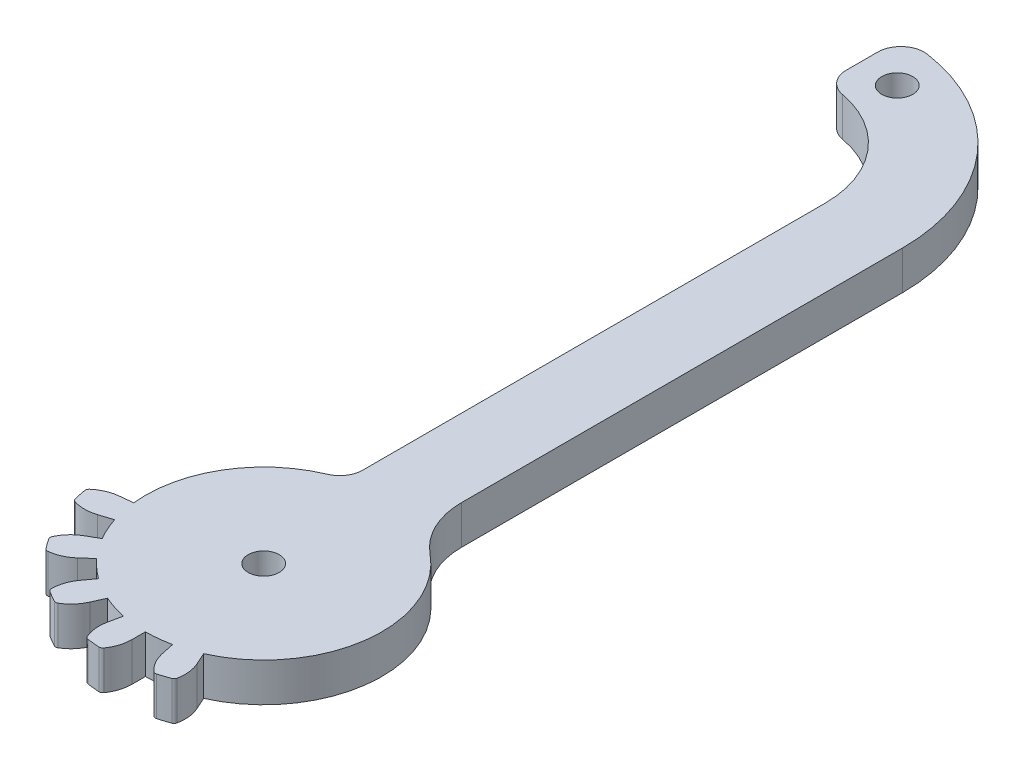
SolidWorks part; units mm, degrees
ref_plane "Front Plane" through (0, 0, 0) normal (0, 0, 1) x (1, 0, 0)
ref_plane "Top Plane" through (0, 0, 0) normal (0, 1, 0) x (1, 0, 0)
ref_plane "Right Plane" through (0, 0, 0) normal (1, 0, 0) x (0, 0, -1)
sketch "Sketch1" plane through (0, 0, 0) normal (0, 1, 0) x (1, 0, 0)
  line L1 (-4.0461, -7.1956) -> (-4.0461, 54.5906)
  line L2 (5.9539, -7.8588) -> (5.9539, 54.5906)
  line L3 (-15.1764, -23.5045) -> (-16.9069, -23.6864)
  line L4 (-14.5131, -26.625) -> (-16.168, -27.1627)
  line L6 (-13.2155, -29.5394) -> (-14.7224, -30.4094)
  line L7 (-11.3404, -32.1203) -> (-12.6335, -33.2846)
  line L11 (-8.9696, -34.255) -> (-9.9923, -35.6627)
  line L12 (-6.2068, -35.8501) -> (-6.9145, -37.4397)
  line L14 (-17.5461, 78.0906) -> (-17.5461, 68.0906)
  line L15 (-3.1727, -36.8359) -> (-3.5345, -38.5379)
  line L16 (0, -37.1694) -> (0, -38.9094)
  line L19 (3.1727, -36.8359) -> (3.5345, -38.5379)
  line L20 (6.2068, -35.8501) -> (6.9145, -37.4397)
  line L29 (13.2155, -29.5394) -> (14.7224, -30.4094) [skipped]
  line L30 (11.3404, -32.1203) -> (12.6335, -33.2846) [skipped]
  line L31 (8.9696, -34.255) -> (9.9923, -35.6627) [skipped]
  line L32 (14.5131, -26.625) -> (16.168, -27.1627) [skipped]
  arc A0 (-15.26, -21.9094) -> (-15.1764, -23.5045) centre (0, -21.9094) ccw
  arc A1 (-19.7538, -25.0381) -> (-19.3185, -27.0858) centre (0, -21.9094) ccw
  arc A2 (-13.9407, -28.1162) -> (-13.2155, -29.5394) centre (0, -21.9094) ccw
  arc A3 (-16.9069, -23.6864) -> (-19.7538, -25.0381) centre (-16.411, -28.4047) ccw
  arc A4 (-16.168, -27.1627) -> (-19.3185, -27.0858) centre (-17.634, -22.6506) cw
  arc A5 (-14.5131, -26.625) -> (-13.9407, -28.1162) centre (0, -21.9094) ccw
  arc A6 (-14.7224, -30.4094) -> (-16.7734, -32.8022) centre (-12.3503, -34.5181) ccw
  arc A7 (-16.7734, -32.8022) -> (-15.5429, -34.4958) centre (0, -21.9094) ccw
  arc A8 (-12.6335, -33.2846) -> (-15.5429, -34.4958) centre (-15.808, -29.7589) cw
  arc A9 (-11.3404, -32.1203) -> (-10.2109, -33.2498) centre (0, -21.9094) ccw
  arc A10 (-10.2109, -33.2498) -> (-8.9696, -34.255) centre (0, -21.9094) ccw
  arc A11 (-9.9923, -35.6627) -> (-10.8928, -38.6828) centre (-6.1541, -38.4513) ccw
  arc A12 (-10.8928, -38.6828) -> (-9.0798, -39.7295) centre (0, -21.9094) ccw
  arc A13 (-6.9145, -37.4397) -> (-9.0798, -39.7295) centre (-11.2487, -35.51) cw
  arc A14 (-6.2068, -35.8501) -> (-4.7156, -36.4225) centre (0, -21.9094) ccw
  arc A15 (-4.7156, -36.4225) -> (-3.1727, -36.8359) centre (0, -21.9094) ccw
  arc A16 (-3.5345, -38.5379) -> (-3.1287, -41.6632) centre (1.1061, -39.5243) ccw
  arc A17 (-3.1287, -41.6632) -> (-1.0467, -41.882) centre (0, -21.9094) ccw
  arc A18 (0, -38.9094) -> (-1.0467, -41.882) centre (-4.7443, -38.9094) cw
  arc A19 (0, -37.1694) -> (1.5951, -37.0858) centre (0, -21.9094) ccw
  arc A20 (1.5951, -37.0858) -> (3.1727, -36.8359) centre (0, -21.9094) ccw
  arc A21 (3.5345, -38.5379) -> (5.1764, -41.2279) centre (8.1751, -37.5515) ccw
  arc A22 (5.1764, -41.2279) -> (7.1674, -40.581) centre (0, -21.9094) ccw
  arc A23 (6.9145, -37.4397) -> (7.1674, -40.581) centre (2.5804, -39.3694) cw
  arc A24 (6.2068, -35.8501) -> (7.63, -35.1249) centre (0, -21.9094) ccw
  arc A25 (7.63, -35.1249) -> (8.9696, -34.255) centre (0, -21.9094) ccw
  circle A27 centre (-12.5461, 72.4021) radius 2
  arc A29 (11.3404, -32.1203) -> (12.3456, -30.879) centre (0, -21.9094) ccw
  arc A30 (12.3456, -30.879) -> (13.2155, -29.5394) centre (0, -21.9094) ccw
  arc A34 (14.5131, -26.625) -> (14.9265, -25.0821) centre (0, -21.9094) ccw
  arc A35 (14.9265, -25.0821) -> (5.8419, -7.8119) centre (0, -21.9094) ccw
  arc A36 (-4.0461, -7.1956) -> (-15.1764, -23.5045) centre (0, -21.9094) ccw
  arc A37 (-17.5461, 68.0906) -> (-4.0461, 54.5906) centre (-17.5461, 54.5906) cw
  arc A38 (-17.5461, 78.0906) -> (5.9539, 54.5906) centre (-17.5461, 54.5906) cw
  arc A39 (-15.1761, -20.3116) -> (-15.26, -21.9094) centre (0, -21.9094) ccw
  circle A40 centre (0, -21.9094) radius 2
  arc A41 (8.9696, -34.255) -> (14.9265, -25.0821) centre (0, -21.9094) ccw
  arc A42 (16.168, -27.1627) -> (18.6716, -29.0768) centre (14.7019, -31.6748) cw [skipped]
  arc A43 (9.9923, -35.6627) -> (12.5864, -37.4523) centre (13.8306, -32.8741) ccw [skipped]
  arc A44 (12.5864, -37.4523) -> (14.1421, -36.0515) centre (0, -21.9094) ccw [skipped]
  arc A45 (12.6335, -33.2846) -> (14.1421, -36.0515) centre (9.4589, -36.8103) cw [skipped]
  arc A46 (14.7224, -30.4094) -> (17.8201, -30.9892) centre (17.0946, -26.3007) ccw [skipped]
  arc A47 (17.8201, -30.9892) -> (18.6716, -29.0768) centre (0, -21.9094) ccw [skipped]
  dimension "D1" = 10
  dimension "D4" = 7
extrude "Boss-Extrude3" add sketch "Sketch1" along normal blind 5
fillet "Fillet9" radius 10 1 edges at (5.9539, 2.5, 7.8588)
fillet "Fillet10" radius 3 1 edges at (-4.0461, 2.5, 7.1956)
fillet "Fillet11" radius 3 1 edges at (-17.5461, 2.5, -78.0906)
fillet "Fillet12" radius 3 1 edges at (-17.5461, 2.5, -68.0906)
fillet "Fillet13" radius 0.5 10 edges at (7.1674, 2.5, 40.581) (5.1764, 2.5, 41.2279) (-1.0467, 2.5, 41.882) (-3.1287, 2.5, 41.6632) (-9.0798, 2.5, 39.7295) (-10.8928, 2.5, 38.6828) (-15.5429, 2.5, 34.4958) (-16.7734, 2.5, 32.8022) (-19.3185, 2.5, 27.0858) (-19.7538, 2.5, 25.0381)
